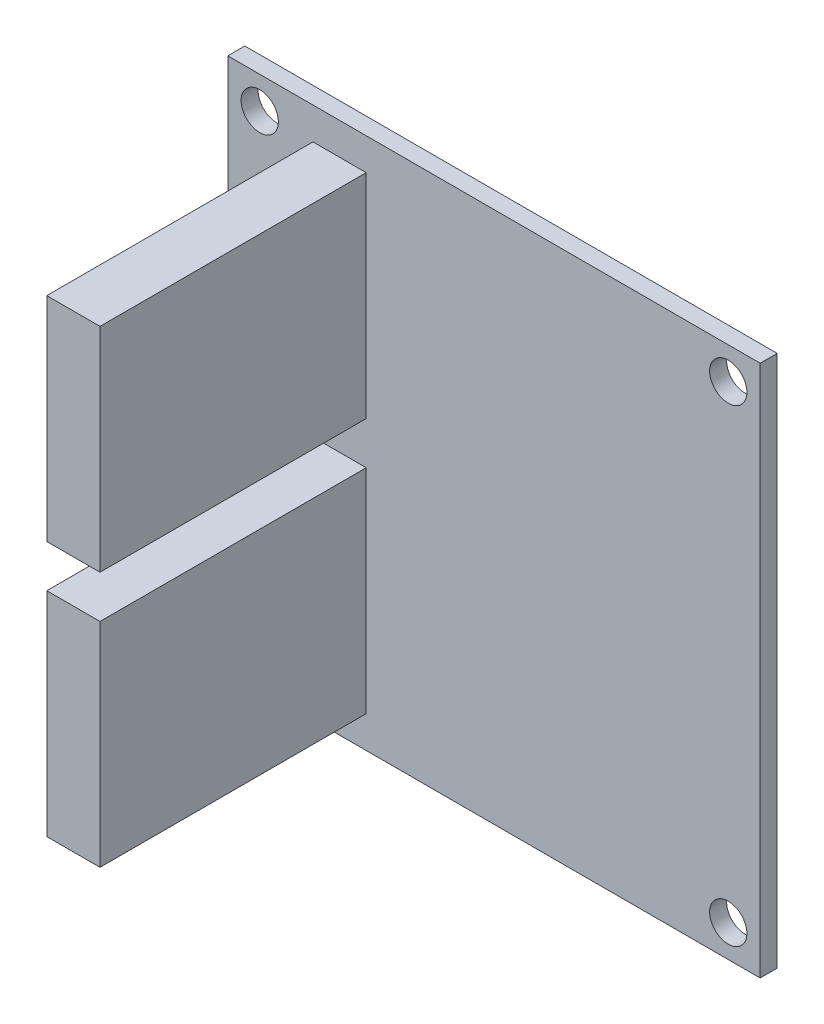
SolidWorks part; units mm, degrees
ref_plane "Front" through (0, 0, 0) normal (0, 0, 1) x (1, 0, 0)
ref_plane "Top" through (0, 0, 0) normal (0, 1, 0) x (1, 0, 0)
ref_plane "Right" through (0, 0, 0) normal (1, 0, 0) x (0, 0, -1)
sketch "Esquisse1" plane through (0, 0, 0) normal (0, 0, 1) x (1, 0, 0)
  line L1 (0, 0) -> (50, 0)
  line L2 (0, 0) -> (0, 50)
  line L3 (0, 50) -> (50, 50)
  line L4 (50, 0) -> (50, 50)
  dimension "D1" = 50
  dimension "D2" = 50
extrude "Boss.-Extru.1" add sketch "Esquisse1" along normal blind 1.6
sketch "Esquisse2" plane through (0, 0, 1.6) normal (0, 0, 1) x (1, 0, 0)
  line L0 (25, 0) -> (25, 25) construction
  line L1 (0, 0) -> (50, 0) construction
  line L2 (25, 25) -> (0, 25) construction
  line L3 (0, 50) -> (0, 0) construction
  circle A0 centre (3, 3) radius 1.75
  circle A1 centre (47, 3) radius 1.75
  circle A2 centre (47, 47) radius 1.75
  circle A3 centre (3, 47) radius 1.75
  dimension "D1" = 3
  dimension "D2" = 3
  dimension "D3" = 3.5
extrude "Enlèv. mat.-Extru.1" cut sketch "Esquisse2" against normal through all both and the other way through all
sketch "Esquisse3" plane through (0, 0, 1.6) normal (0, 0, 1) x (1, 0, 0)
  line L0 (0, 25) -> (2.9728, 25) construction
  line L1 (8, 47) -> (13, 47)
  line L2 (8, 47) -> (8, 27)
  line L3 (8, 27) -> (13, 27)
  line L4 (13, 47) -> (13, 27)
  line L5 (0, 50) -> (0, 0) construction
  line L6 (13, 3) -> (13, 23)
  line L7 (8, 23) -> (13, 23)
  line L8 (8, 3) -> (8, 23)
  line L9 (8, 3) -> (13, 3)
  dimension "D1" = 5
  dimension "D2" = 8
  dimension "D3" = 4
  dimension "D4" = 20
extrude "Boss.-Extru.2" add sketch "Esquisse3" along normal blind 25
